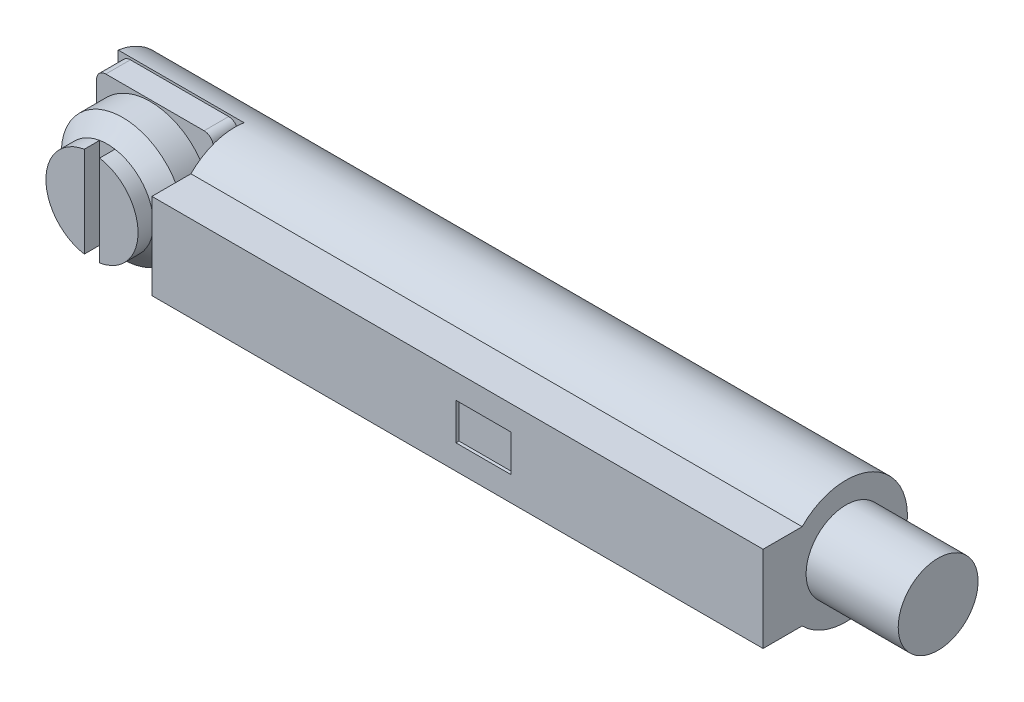
SolidWorks part; units mm, degrees
ref_plane "Front" through (0, 0, 0) normal (0, 0, 1) x (1, 0, 0)
ref_plane "Top" through (0, 0, 0) normal (0, 1, 0) x (1, 0, 0)
ref_plane "Right" through (0, 0, 0) normal (1, 0, 0) x (0, 0, -1)
ref_plane "Plane1" through (0, 0, 0) normal (1, 0, 0) x (0, 0, -1)
sketch "Sketch1" plane through (0, 0, 0) normal (1, 0, 0) x (0, 0, -1)
  line L0 (-2.7, 0.6) -> (-1.4283, 0.6)
  line L1 (-1.4283, 3.4) -> (-2.7, 3.4)
  line L2 (-2.7, 3.4) -> (-2.7, 0.6)
  arc A0 (-1.4283, 0.6) -> (-1.4283, 3.4) centre (0, 2) ccw
extrude "Boss-Extrude1" add sketch "Sketch1" along normal blind 24
ref_plane "Plane2" through (0, 0, 0) normal (1, 0, 0) x (0, 0, -1)
sketch "Sketch2" plane through (0, 0, 0) normal (1, 0, 0) x (0, 0, -1)
  line L0 (-2.7, 0) -> (0.3, 0)
  line L1 (0.3, 0) -> (0.3, 4)
  line L2 (0.3, 4) -> (-2.7, 4)
  line L3 (-2.7, 4) -> (-2.7, 0)
extrude "Cut-Extrude1" cut sketch "Sketch2" along normal blind 4.1
ref_plane "Plane3" through (0, 0, -0.3) normal (0, 0, 1) x (1, 0, 0)
sketch "Sketch3" plane through (0, 0, -0.3) normal (0, 0, 1) x (1, 0, 0)
  line L0 (0.4, 0.1) -> (3.6, 0.1)
  line L1 (3.9, 0.4) -> (3.9, 3.6)
  line L2 (3.6, 3.9) -> (0.4, 3.9)
  line L3 (0.1, 3.6) -> (0.1, 0.4)
  arc A0 (0.1, 0.4) -> (0.4, 0.1) centre (0.4, 0.4) ccw
  arc A1 (3.6, 0.1) -> (3.9, 0.4) centre (3.6, 0.4) ccw
  arc A2 (3.9, 3.6) -> (3.6, 3.9) centre (3.6, 3.6) ccw
  arc A3 (0.4, 3.9) -> (0.1, 3.6) centre (0.4, 3.6) ccw
extrude "Boss-Extrude2" add sketch "Sketch3" along normal blind 0.8
ref_plane "Plane4" through (0, 2, 0) normal (0, 1, 0) x (-1, 0, 0)
sketch "Sketch4" plane through (0, 2, 0) normal (0, 1, 0) x (-1, 0, 0)
  line L0 (-2, 2.55) -> (-0.5, 2.55)
  line L1 (-0.5, 2.55) -> (-0.5, 2.05)
  line L2 (-0.5, 2.05) -> (0, 1.55)
  line L3 (0, 1.55) -> (0, 0.65)
  line L4 (0, 0.65) -> (-1.25, 0.65)
  line L5 (-1.25, 0.65) -> (-1.25, 0.3)
  line L6 (-1.25, 0.3) -> (-2, 0.3)
  line L7 (-2, 0.3) -> (-2, 2.55)
  line L8 (-2, 0.3) -> (-2, 2.55) construction
revolve "Revolve1" add sketch "Sketch4" angle 360 about L8
ref_plane "Plane5" through (0, 2, 0) normal (0, 1, 0) x (-1, 0, 0)
sketch "Sketch5" plane through (0, 2, 0) normal (0, 1, 0) x (-1, 0, 0)
  line L0 (-1.75, 2.55) -> (-2.25, 2.55)
  line L1 (-2.25, 2.55) -> (-2.25, 2.05)
  line L2 (-2.25, 2.05) -> (-1.75, 2.05)
  line L3 (-1.75, 2.05) -> (-1.75, 2.55)
extrude "Cut-Extrude2" cut sketch "Sketch5" against normal blind 2 and the other way blind 2
ref_plane "Plane6" through (0, 0, 2.7) normal (0, 0, 1) x (1, 0, 0)
sketch "Sketch6" plane through (0, 0, 2.7) normal (0, 0, 1) x (1, 0, 0)
  line L0 (14, 1.4) -> (15.8, 1.4)
  line L1 (15.8, 1.4) -> (15.8, 2.6)
  line L2 (15.8, 2.6) -> (14, 2.6)
  line L3 (14, 2.6) -> (14, 1.4)
extrude "Cut-Extrude3" cut sketch "Sketch6" against normal blind 0.1
ref_plane "Plane7" through (0, 2, 0) normal (0, 1, 0) x (-1, 0, 0)
sketch "Sketch7" plane through (0, 2, 0) normal (0, 1, 0) x (-1, 0, 0)
  line L0 (-24, 0) -> (-24, -1.3)
  line L1 (-24, -1.3) -> (-27, -1.3)
  line L2 (-27, -1.3) -> (-27, 0)
  line L3 (-27, 0) -> (-24, 0)
  line L4 (-27, 0) -> (-24, 0) construction
revolve "Revolve2" add sketch "Sketch7" angle 360 about L4
